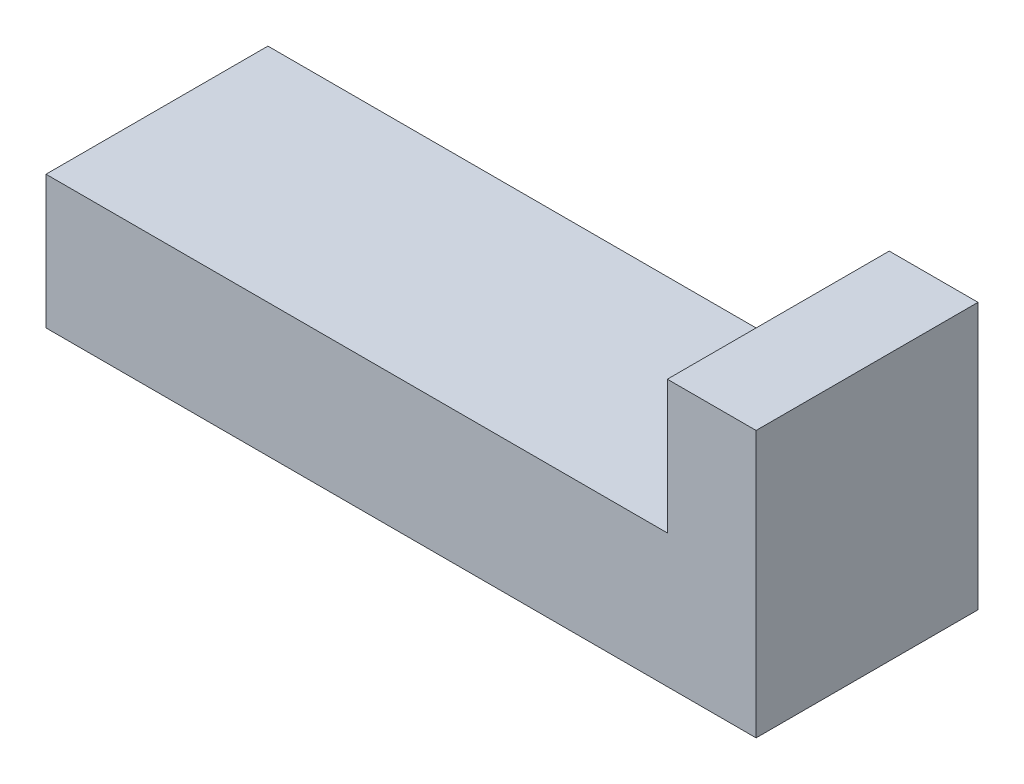
SolidWorks part; units mm, degrees
ref_plane "Front Plane" through (0, 0, 0) normal (0, 0, 1) x (1, 0, 0)
ref_plane "Top Plane" through (0, 0, 0) normal (0, 1, 0) x (1, 0, 0)
ref_plane "Right Plane" through (0, 0, 0) normal (1, 0, 0) x (0, 0, -1)
sketch "Sketch1" plane through (0, 0, 0) normal (0, 0, 1) x (1, 0, 0)
  line L0 (0, 0) -> (16, 0)
  line L1 (16, 0) -> (16, 6)
  line L2 (16, 6) -> (14, 6)
  line L3 (14, 6) -> (14, 3)
  line L4 (14, 3) -> (0, 3)
  line L5 (0, 3) -> (0, 0)
  point P7 (0, 0)
  dimension "D1" = 16
  dimension "D2" = 3
  dimension "D3" = 14
  dimension "D4" = 6
  dimension "D5" = 2
extrude "Boss-Extrude1" add sketch "Sketch1" along normal blind 5
